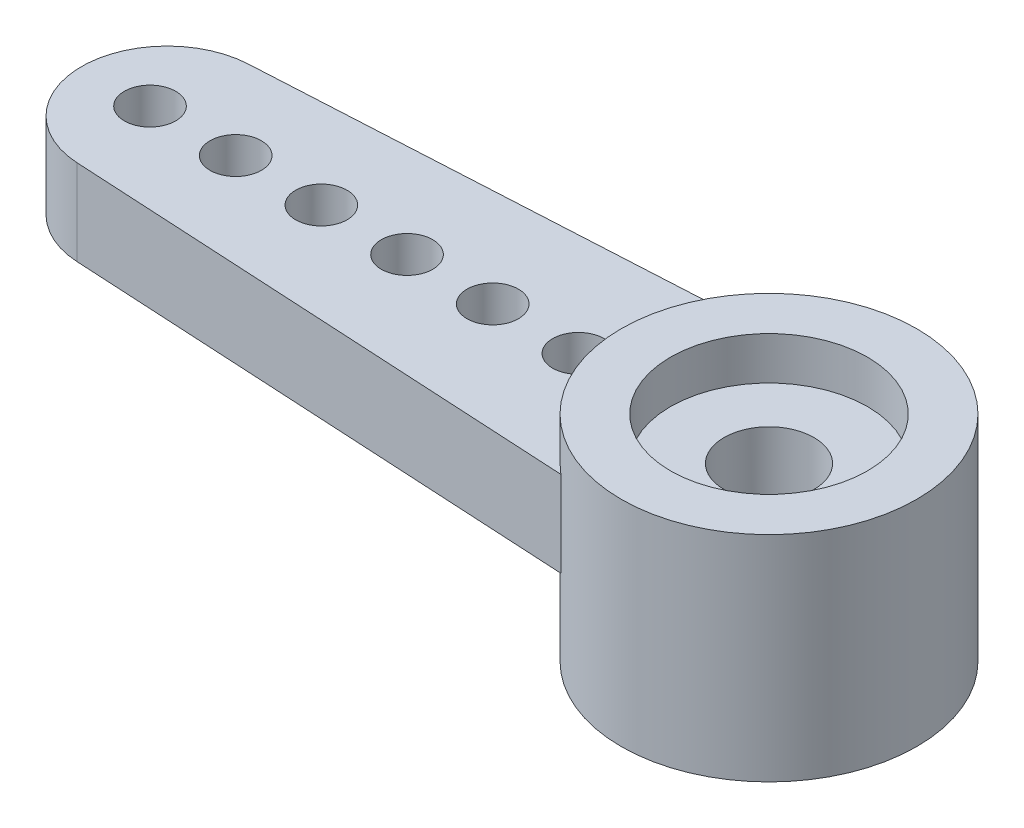
SolidWorks part; units mm, degrees
material "PVC Rígido"
ref_plane "Plano frontal" through (0, 0, 0) normal (0, 0, 1) x (1, 0, 0)
ref_plane "Plano superior" through (0, 0, 0) normal (0, 1, 0) x (1, 0, 0)
ref_plane "Plano direito" through (0, 0, 0) normal (1, 0, 0) x (0, 0, -1)
sketch "Esboço1" plane through (0, 0, 0) normal (0, 1, 0) x (1, 0, 0)
  line L0 (0, 0) -> (-14.05, 0) construction
  line L1 (-14.1591, 1.997) -> (-2.2091, 2.65)
  line L2 (-2.2091, -2.65) -> (-14.1591, -1.997)
  arc A0 (-2.2091, -2.65) -> (-2.2091, 2.65) centre (0, 0) ccw
  arc A1 (-14.1591, 1.997) -> (-14.1591, -1.997) centre (-14.05, 0) ccw
  dimension "D1" = 6.9
  dimension "D2" = 4
  dimension "D3" = 19.5
  dimension "D4" = 5.3
extrude "Ressalto-extrusão1" add sketch "Esboço1" against normal blind 2
sketch "Esboço2" plane through (0, -2, 0) normal (0, -1, 0) x (1, 0, 0)
  arc A0 (-2.2091, -2.65) -> (-2.2091, 2.65) centre (0, 0) ccw construction
  circle A1 centre (0, 0) radius 3.45
extrude "Ressalto-extrusão2" add sketch "Esboço2" along normal offset from surface (3 mm away) 5 up to face at (-7.242, 0, 0)
hole_wizard "Furo4" positions "Esboço9" profile "Esboço10" legacy end condition through all
sketch "Esboço9" plane through (0, 0, 0) normal (0, 1, 0) x (1, 0, 0)
  line L1 (-14.45, 0) -> (0, 0) construction
  arc A2 (-14.1591, 1.997) -> (-14.1591, -1.997) centre (-14.05, 0) ccw construction
  point P0 (-14.45, 0)
  point P19 (-16.05, 0)
  dimension "D1" = 1.6
sketch "Esboço10" plane through (-14.45, 0, 0) normal (1, 0, 0) x (0, 0, 1)
  line L0 (0, 0) -> (0, 5)
  line L1 (0, 5) -> (0.6, 5)
  line L2 (0.6, 5) -> (0.6, 0)
  line L3 (0.6, 0) -> (0, 0)
  line L4 (0, 110) -> (0, -10) construction
  dimension "Diameter" = 1.2
  dimension "Depth" = 5
pattern_linear "Padrão linear1" count 6 spacing 2 along (1, 0, 0) of "Furo4"
hole_wizard "Furo1" positions "Esboço3" profile "Esboço4" legacy
sketch "Esboço3" plane through (0, -5, 0) normal (0, -1, 0) x (-1, 0, 0)
  point P0 (0, 0)
sketch "Esboço4" plane through (0, -5, 0) normal (1, 0, 0) x (0, 0, -1)
  line L0 (0, 0) -> (0, 2)
  line L1 (0, 2) -> (2.475, 2)
  line L2 (2.475, 2) -> (2.475, 0)
  line L3 (2.475, 0) -> (0, 0)
  line L4 (0, 110) -> (0, -10) construction
  dimension "Diameter" = 4.95
  dimension "Depth" = 2
hole_wizard "Furo2" positions "Esboço5" profile "Esboço6" legacy
sketch "Esboço5" plane through (0, 0, 0) normal (0, 1, 0) x (1, 0, 0)
  point P0 (0, 0)
sketch "Esboço6" plane through (0, 0, 0) normal (1, 0, 0) x (0, 0, 1)
  line L0 (0, 0) -> (0, 1)
  line L1 (0, 1) -> (2.3, 1)
  line L2 (2.3, 1) -> (2.3, 0)
  line L3 (2.3, 0) -> (0, 0)
  line L4 (0, 110) -> (0, -10) construction
  dimension "Diameter" = 4.6
  dimension "Depth" = 1
hole_wizard "Furo3" positions "Esboço7" profile "Esboço8" legacy end condition through all
sketch "Esboço7" plane through (0, 0, 0) normal (0, 1, 0) x (1, 0, 0)
  point P0 (0, 0)
sketch "Esboço8" plane through (0, 0, 0) normal (1, 0, 0) x (0, 0, 1)
  line L0 (0, 0) -> (0, 5)
  line L1 (0, 5) -> (1.05, 5)
  line L2 (1.05, 5) -> (1.05, 0)
  line L3 (1.05, 0) -> (0, 0)
  line L4 (0, 110) -> (0, -10) construction
  dimension "Diameter" = 2.1
  dimension "Depth" = 5
sketch "Esboço11" plane through (0, -5, 0) normal (0, -1, 0) x (1, 0, 0)
  line L0 (-0.0981, 2.4731) -> (0, 2.375)
  line L1 (0, 2.375) -> (0.0981, 2.4731)
  line L2 (0, 0) -> (0, 2.475) construction
  circle A0 centre (0, 0) radius 2.375 construction
  circle A1 centre (0, 0) radius 2.475
  arc A2 (0.0981, 2.4731) -> (-0.0981, 2.4731) centre (0, 0) ccw
  dimension "D3" = 4.75
  dimension "D2" = 0.1
  dimension "D1" = 0
extrude "Ressalto-extrusão3" add sketch "Esboço11" against normal up to surface (2 mm away) up to face at (0, -3, 1.05)
pattern_circular "PadrãoCircular1" count 60 over 360 about axis through (0, 0, 0) along (0, 1, 0) of "Ressalto-extrusão3"
sketch "草图1" plane through (0, -2, 0) normal (0, -1, 0) x (1, 0, 0)
  line L2 (-2.2091, 2.65) -> (-14.1591, 1.997)
  line L3 (-14.1591, -1.997) -> (-2.2091, -2.65)
  line L4 (-2.2091, 2.65) -> (-14.1591, 1.997)
  line L5 (-14.1591, -1.997) -> (-2.2091, -2.65)
  arc A2 (-2.2091, 2.65) -> (-2.2091, -2.65) centre (0, 0) ccw
  arc A3 (-14.1591, 1.997) -> (-14.1591, -1.997) centre (-14.05, 0) ccw
  arc A4 (-2.2091, 2.65) -> (-2.2091, -2.65) centre (0, 0) ccw
  arc A5 (-14.1591, 1.997) -> (-14.1591, -1.997) centre (-14.05, 0) ccw
  dimension "D1" = 0
extrude "凸台-拉伸1" add sketch "草图1" along normal blind 1
sketch "草图2" plane through (0, 0, 0) normal (0, 1, 0) x (1, 0, 0)
  line L2 (-14.1591, -1.997) -> (-2.2091, -2.65)
  line L3 (-2.2091, 2.65) -> (-14.1591, 1.997)
  line L4 (-14.1591, -1.997) -> (-2.2091, -2.65)
  line L5 (-2.2091, 2.65) -> (-14.1591, 1.997)
  arc A2 (-2.2091, 2.65) -> (-2.2091, -2.65) centre (0, 0) ccw
  arc A3 (-14.1591, 1.997) -> (-14.1591, -1.997) centre (-14.05, 0) ccw
  arc A4 (-2.2091, 2.65) -> (-2.2091, -2.65) centre (0, 0) ccw
  arc A5 (-14.1591, 1.997) -> (-14.1591, -1.997) centre (-14.05, 0) ccw
  dimension "D1" = 0
extrude "切除-拉伸1" cut sketch "草图2" against normal blind 1
sketch "草图3" plane through (0, -1, 0) normal (0, 1, 0) x (1, 0, 0)
  circle A0 centre (-4.45, 0) radius 0.6 construction
  circle A1 centre (-6.45, 0) radius 0.6 construction
  circle A2 centre (-8.45, 0) radius 0.6 construction
  circle A3 centre (-14.45, 0) radius 0.6 construction
  circle A4 centre (-10.45, 0) radius 0.6 construction
  circle A5 centre (-12.45, 0) radius 0.6 construction
  circle A6 centre (-4.45, 0) radius 0.6
  circle A7 centre (-6.45, 0) radius 0.6
  circle A8 centre (-8.45, 0) radius 0.6
  circle A9 centre (-14.45, 0) radius 0.6
  circle A10 centre (-10.45, 0) radius 0.6
  circle A11 centre (-12.45, 0) radius 0.6
extrude "切除-拉伸2" cut sketch "草图3" against normal through all
